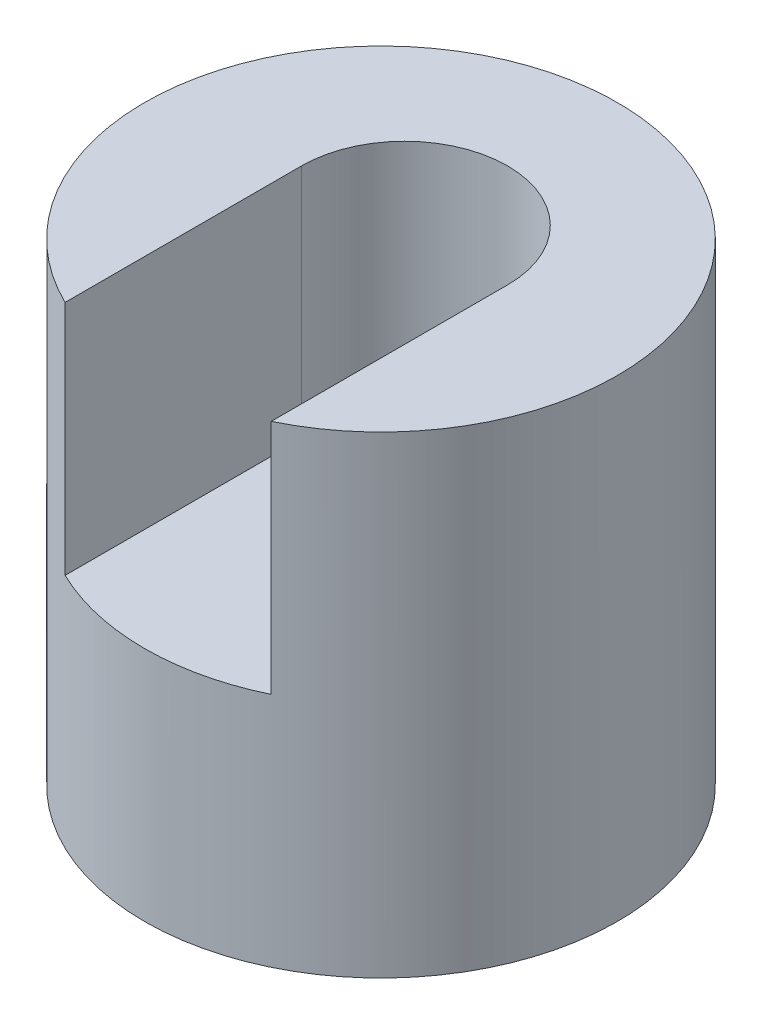
SolidWorks part; units mm, degrees
ref_plane "Front Plane" through (0, 0, 0) normal (0, 0, 1) x (1, 0, 0)
ref_plane "Top Plane" through (0, 0, 0) normal (0, 1, 0) x (1, 0, 0)
ref_plane "Right Plane" through (0, 0, 0) normal (1, 0, 0) x (0, 0, -1)
sketch "Sketch1" plane through (0, 0, 0) normal (0, 0, 1) x (1, 0, 0)
  line L1 (0, 0) -> (40, 0)
  line L2 (0, 0) -> (0, 40)
  line L3 (0, 40) -> (40, 40)
  line L4 (40, 0) -> (40, 40)
  dimension "D1" = 40
  dimension "D2" = 40
extrude "Boss-Extrude1" add sketch "Sketch1" along normal blind 40
sketch "Sketch2" plane through (0, 40, 0) normal (0, 1, 0) x (1, 0, 0)
  line L1 (40, 0) -> (0, 0) construction
  line L2 (40, -40) -> (40, 0) construction
  line L3 (0, 0) -> (40, 0)
  line L4 (40, 0) -> (40, -40)
  line L5 (40, -40) -> (0, -40)
  line L6 (0, -40) -> (0, 0)
  circle A0 centre (20, -20) radius 20
  line M1 (40, 0) -> (0, 0)
  line M2 (0, 0) -> (0, -40)
  line M3 (0, -40) -> (40, -40)
  line M4 (40, -40) -> (40, 0)
  dimension "D1" = 40
  dimension "D2" = 20
  dimension "D3" = 20
extrude "Cut-Extrude1" cut sketch "Sketch2" against normal blind 40 contours A0 L3 M2 | A0 L4 M1 | A0 L5 M4 | A0 L6 M3
sketch "Sketch3" plane through (0, 0, 0) normal (1, 0, 0) x (0, 0, -1)
  line L1 (-40, 40) -> (-38, 40)
  line L2 (-40, 40) -> (-40, 20)
  line L3 (-40, 20) -> (-38, 20)
  line L4 (-38, 40) -> (-38, 20)
  dimension "D1" = 2
  dimension "D2" = 20
extrude "Cut-Extrude2" cut sketch "Sketch3" along normal blind 40
sketch "Sketch4" plane through (0, 40, 0) normal (0, 1, 0) x (1, 0, 0)
  line L0 (11.2822, -38) -> (11.2822, -18)
  line L1 (28.7178, -38) -> (28.7178, -18)
  line L2 (11.2822, -38) -> (28.7178, -38)
  arc A0 (28.7178, -18) -> (11.2822, -18) centre (20, -18) ccw
  dimension "D1" = 20
  dimension "D2" = 20
extrude "Cut-Extrude3" cut sketch "Sketch4" against normal blind 20
